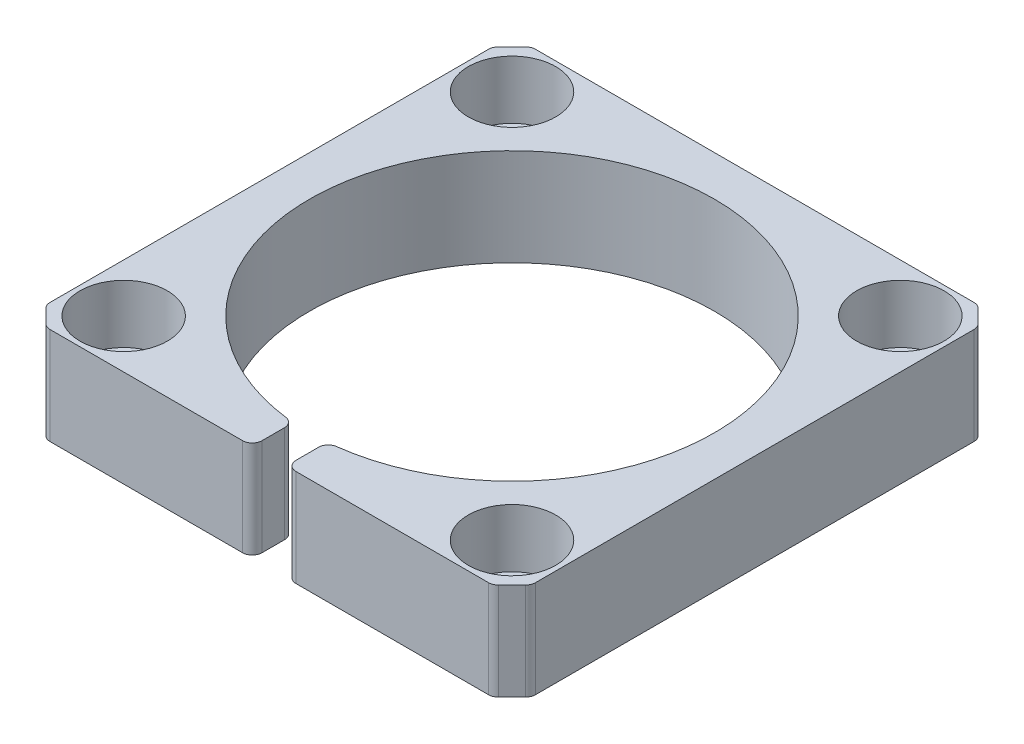
SolidWorks part; units mm, degrees
ref_plane "Front Plane" through (0, 0, 0) normal (0, 0, 1) x (1, 0, 0)
ref_plane "Top Plane" through (0, 0, 0) normal (0, 1, 0) x (1, 0, 0)
ref_plane "Right Plane" through (0, 0, 0) normal (1, 0, 0) x (0, 0, -1)
sketch "Sketch1" plane through (0, 0, 0) normal (0, 1, 0) x (1, 0, 0)
  line L1 (-25, -25) -> (25, -25)
  line L2 (-25, -25) -> (-25, 25)
  line L3 (-25, 25) -> (25, 25)
  line L4 (25, -25) -> (25, 25)
  line L5 (-25, -25) -> (25, 25) construction
  line L6 (-25, 25) -> (25, -25) construction
  circle A0 centre (0, 0) radius 20.85
  dimension "D1" = 41.7
  dimension "D2" = 50
  dimension "D3" = 50
extrude "Boss-Extrude1" add sketch "Sketch1" along normal blind 10
sketch "Sketch2" plane through (0, 10, 0) normal (0, 1, 0) x (1, 0, 0)
  line L0 (0, 0) -> (0, -28.1223) construction
  line L1 (-25, -25) -> (25, -25) construction
  line L2 (-1.75, -31.0618) -> (1.75, -31.0618)
  line L3 (-1.75, -31.0618) -> (-1.75, -18.9382)
  line L4 (-1.75, -18.9382) -> (1.75, -18.9382)
  line L5 (1.75, -31.0618) -> (1.75, -18.9382)
  line L6 (-1.75, -31.0618) -> (1.75, -18.9382) construction
  line L7 (-1.75, -18.9382) -> (1.75, -31.0618) construction
  point P3 (0, -25)
  dimension "D1" = 3.5
extrude "Cut-Extrude1" cut sketch "Sketch2" against normal blind 10
chamfer "Chamfer1" distance 2 angle 45 4 edges at (-25, 5, -25) (-25, 5, 25) (25, 5, -25) (25, 5, 25)
fillet "Fillet1" radius 1 12 edges at (23, 5, -25) (25, 5, -23) (25, 5, 23) (23, 5, 25) (1.75, 5, 20.7764) (1.75, 5, 25) (-23, 5, -25) (-25, 5, -23) (-25, 5, 23) (-23, 5, 25) (-1.75, 5, 20.7764) (-1.75, 5, 25)
sketch "Sketch3" plane through (0, 10, 0) normal (0, 1, 0) x (1, 0, 0)
  line L0 (0, -34.533) -> (0, 34.533) construction
  line L1 (0, 0) -> (-25, 0) construction
  line L2 (-25, 22.5858) -> (-25, -22.5858) construction
  circle A0 centre (-20, 20) radius 3.4159
  circle A1 centre (20, 20) radius 3.4159
  circle A2 centre (20, -20) radius 3.4159
  circle A3 centre (-20, -20) radius 3.4159
  point P4 (0, 0)
  dimension "D1" = 20
  dimension "D2" = 20
hole_wizard "Ø5.2 (5.2) Diameter Hole1" positions "3DSketch1" profile "Sketch4" hole size "Ø5.2" standard "GB"
sketch3d "3DSketch1"
  point P0 (-20, 10, -20)
  point P3 (20, 10, -20)
  point P6 (20, 10, 20)
  point P9 (-20, 10, 20)
sketch "Sketch4" plane through (-20, 10, -20) normal (1, 0, 0) x (0, 0, 1)
  line L0 (0, 0) -> (0, 11.5622)
  line L1 (0, 11.5622) -> (2.6, 10)
  line L2 (2.6, 10) -> (2.6, 0)
  line L5 (2.6, 0) -> (0, 0)
  line L10 (0, 11.5622) -> (-2.6, 10) construction
  line L11 (0, -6.35) -> (0, 107.95) construction
  dimension "Hole Dia." = 5.2
  dimension "Hole Depth" = 10
  dimension "Drill Angle" = 118
hole_wizard "CBORE for M5 Hex Socket Head Cap Screw1" positions "3DSketch2" profile "Sketch5" counterbore size "M5" standard "ISO" end condition through all
sketch3d "3DSketch2"
  point P0 (-20, 10, -20)
  point P3 (-20, 10, 20)
  point P6 (20, 10, 20)
  point P9 (20, 10, -20)
sketch "Sketch5" plane through (-20, 10, -20) normal (1, 0, 0) x (0, 0, 1)
  line L0 (0, 0) -> (0, 10)
  line L1 (0, 10) -> (2.75, 10)
  line L3 (2.75, 10) -> (2.75, 6)
  line L4 (2.75, 6) -> (4.5, 6)
  line L5 (4.5, 6) -> (4.5, 0)
  line L7 (4.5, 0) -> (0, 0)
  line L11 (0, -6.35) -> (0, 107.95) construction
  dimension "Thru Hole Dia." = 5.5
  dimension "Thru Hole Depth" = 10
  dimension "C'Bore Dia." = 9
  dimension "C'Bore Depth" = 6
